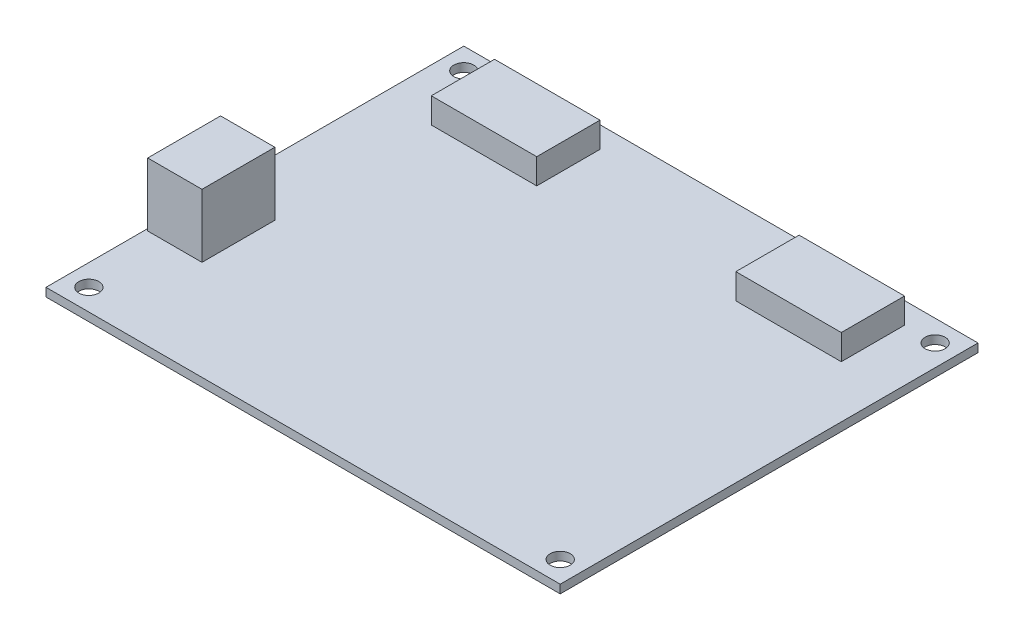
SolidWorks part; units mm, degrees
ref_plane "Front Plane" through (0, 0, 0) normal (0, 0, 1) x (1, 0, 0)
ref_plane "Top Plane" through (0, 0, 0) normal (0, 1, 0) x (1, 0, 0)
ref_plane "Right Plane" through (0, 0, 0) normal (1, 0, 0) x (0, 0, -1)
sketch "Sketch1" plane through (0, 0, 0) normal (0, 1, 0) x (1, 0, 0)
  line L0 (-154.2746, 0) -> (133.8872, 0) construction
  line L1 (0, 57.5106) -> (0, -34.9932) construction
  line L3 (60.96, 49.53) -> (-60.96, 49.53)
  line L4 (60.96, 49.53) -> (60.96, -49.53)
  line L5 (60.96, -49.53) -> (-60.96, -49.53)
  line L6 (-60.96, 49.53) -> (-60.96, -49.53)
  line L7 (60.96, 49.53) -> (-60.96, -49.53) construction
  line L8 (60.96, -49.53) -> (-60.96, 49.53) construction
  point P4 (0, 0)
extrude "Boss-Extrude1" add sketch "Sketch1" along normal blind 2
sketch "Sketch2" plane through (0, 2, 0) normal (0, 1, 0) x (1, 0, 0)
  line L0 (0, 29.2995) -> (0, -17.9523) construction
  line L1 (20.3233, 0) -> (-25.7429, 0) construction
  line L2 (-60.96, 49.53) -> (-60.96, -49.53) construction
  line L3 (60.96, 49.53) -> (-60.96, 49.53) construction
  circle A0 centre (-55.88, 44.45) radius 2.3711
  circle A1 centre (55.88, 44.45) radius 2.3711
  circle A2 centre (55.88, -44.45) radius 2.3711
  circle A3 centre (-55.88, -44.45) radius 2.3711
  dimension "D1" = 5.08
  dimension "D2" = 5.08
extrude "Cut-Extrude1" cut sketch "Sketch2" against normal blind 2
sketch "Sketch3" plane through (0, 2, 0) normal (0, 1, 0) x (1, 0, 0)
  line L0 (0, 52.3326) -> (0, -52.1632) construction
  line L1 (-48.6066, 44.4688) -> (-23.6066, 44.4688)
  line L2 (-48.6066, 44.4688) -> (-48.6066, 29.4688)
  line L3 (-48.6066, 29.4688) -> (-23.6066, 29.4688)
  line L4 (-23.6066, 44.4688) -> (-23.6066, 29.4688)
  line L5 (-48.6066, 44.4688) -> (-23.6066, 29.4688) construction
  line L6 (-48.6066, 29.4688) -> (-23.6066, 44.4688) construction
  line L7 (48.6066, 29.4688) -> (23.6066, 44.4688) construction
  line L8 (48.6066, 44.4688) -> (23.6066, 29.4688) construction
  line L9 (23.6066, 44.4688) -> (23.6066, 29.4688)
  line L10 (48.6066, 29.4688) -> (23.6066, 29.4688)
  line L11 (48.6066, 44.4688) -> (48.6066, 29.4688)
  line L12 (48.6066, 44.4688) -> (23.6066, 44.4688)
  point P0 (-36.1066, 36.9688)
  point P12 (36.1066, 36.9688)
extrude "Boss-Extrude2" add sketch "Sketch3" along normal blind 6
sketch "Sketch4" plane through (0, 2, 0) normal (0, 1, 0) x (1, 0, 0)
  line L1 (-60.4619, -8.6374) -> (-47.5904, -8.6374)
  line L2 (-60.4619, -8.6374) -> (-60.4619, -25.9122)
  line L3 (-60.4619, -25.9122) -> (-47.5904, -25.9122)
  line L4 (-47.5904, -8.6374) -> (-47.5904, -25.9122)
  line L5 (-60.4619, -8.6374) -> (-47.5904, -25.9122) construction
  line L6 (-60.4619, -25.9122) -> (-47.5904, -8.6374) construction
  point P0 (-54.0262, -17.2748)
extrude "Boss-Extrude3" add sketch "Sketch4" along normal blind 15
equation "\"D2@Sketch2\"=\"D1@Sketch2\""
